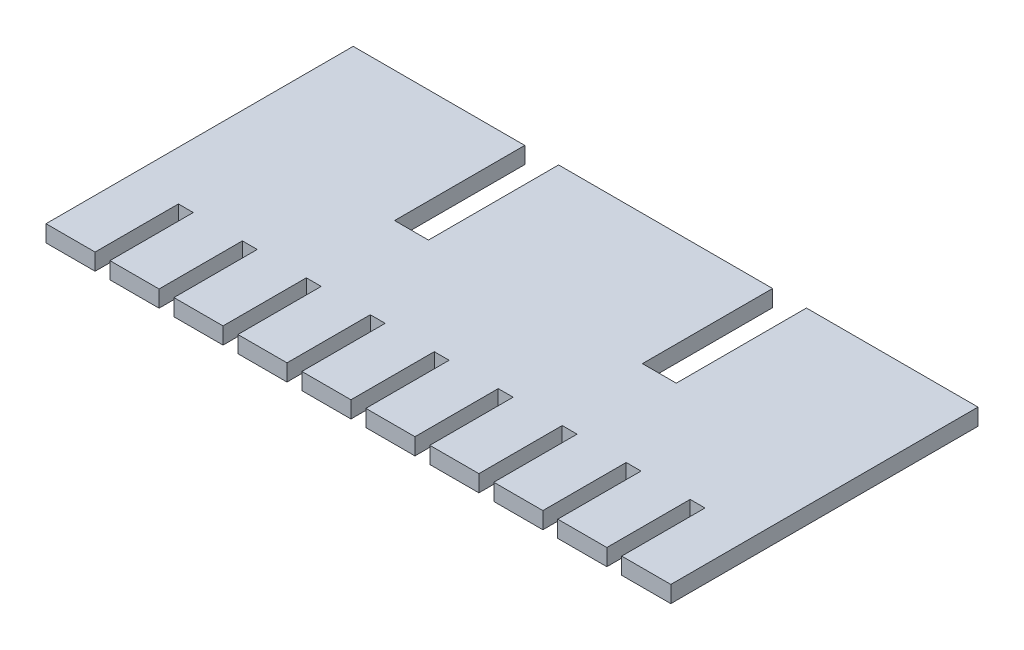
SolidWorks part; units mm, degrees
ref_plane "Front Plane" through (0, 0, 0) normal (0, 0, 1) x (1, 0, 0)
ref_plane "Top Plane" through (0, 0, 0) normal (0, 1, 0) x (1, 0, 0)
ref_plane "Right Plane" through (0, 0, 0) normal (1, 0, 0) x (0, 0, -1)
sketch "Sketch1" plane through (0, 0, 0) normal (0, 1, 0) x (1, 0, 0)
  line L0 (0, 0) -> (0, -29.5)
  line L1 (0, -29.5) -> (4.7139, -29.5)
  line L2 (4.7139, -29.5) -> (4.7139, -21.5)
  line L3 (4.7139, -21.5) -> (6.1429, -21.5)
  line L4 (6.1429, -21.5) -> (6.1429, -29.5)
  line L5 (6.1429, -29.5) -> (10.8568, -29.5)
  line L6 (10.8568, -29.5) -> (10.8568, -21.5)
  line L7 (10.8568, -21.5) -> (12.2858, -21.5)
  line L8 (12.2858, -21.5) -> (12.2858, -29.5)
  line L9 (12.2858, -29.5) -> (16.9997, -29.5)
  line L10 (16.9997, -29.5) -> (16.9997, -21.5)
  line L11 (16.9997, -21.5) -> (18.4287, -21.5)
  line L12 (18.4287, -21.5) -> (18.4287, -29.5)
  line L13 (18.4287, -29.5) -> (23.1426, -29.5)
  line L14 (23.1426, -29.5) -> (23.1426, -21.5)
  line L15 (23.1426, -21.5) -> (24.5716, -21.5)
  line L16 (24.5716, -21.5) -> (24.5716, -29.5)
  line L17 (24.5716, -29.5) -> (29.2855, -29.5)
  line L18 (29.2855, -29.5) -> (29.2855, -21.5)
  line L19 (29.2855, -21.5) -> (30.7145, -21.5)
  line L20 (30.7145, -21.5) -> (30.7145, -29.5)
  line L21 (30.7145, -29.5) -> (35.4284, -29.5)
  line L22 (35.4284, -29.5) -> (35.4284, -21.5)
  line L23 (35.4284, -21.5) -> (36.8574, -21.5)
  line L24 (36.8574, -21.5) -> (36.8574, -29.5)
  line L25 (36.8574, -29.5) -> (41.5713, -29.5)
  line L26 (41.5713, -29.5) -> (41.5713, -21.5)
  line L27 (41.5713, -21.5) -> (43.0003, -21.5)
  line L28 (43.0003, -21.5) -> (43.0003, -29.5)
  line L29 (43.0003, -29.5) -> (47.7142, -29.5)
  line L30 (47.7142, -29.5) -> (47.7142, -21.5)
  line L31 (47.7142, -21.5) -> (49.1432, -21.5)
  line L32 (49.1432, -21.5) -> (49.1432, -29.5)
  line L33 (49.1432, -29.5) -> (53.8571, -29.5)
  line L34 (53.8571, -29.5) -> (53.8571, -21.5)
  line L35 (53.8571, -21.5) -> (55.2861, -21.5)
  line L36 (55.2861, -21.5) -> (55.2861, -29.5)
  line L37 (55.2861, -29.5) -> (60, -29.5)
  line L38 (60, -29.5) -> (60, 0)
  line L39 (60, 0) -> (43.525, 0)
  line L48 (43.525, 0) -> (43.525, -12.5)
  line L49 (43.525, -12.5) -> (40.275, -12.5)
  line L50 (40.275, -12.5) -> (40.275, 0)
  line L51 (40.275, 0) -> (19.725, 0)
  line L52 (19.725, 0) -> (19.725, -12.5)
  line L53 (19.725, -12.5) -> (16.475, -12.5)
  line L54 (16.475, -12.5) -> (16.475, 0)
  line L55 (0, 0) -> (16.475, 0)
extrude "Boss-Extrude3" add sketch "Sketch1" along normal blind 1.6
